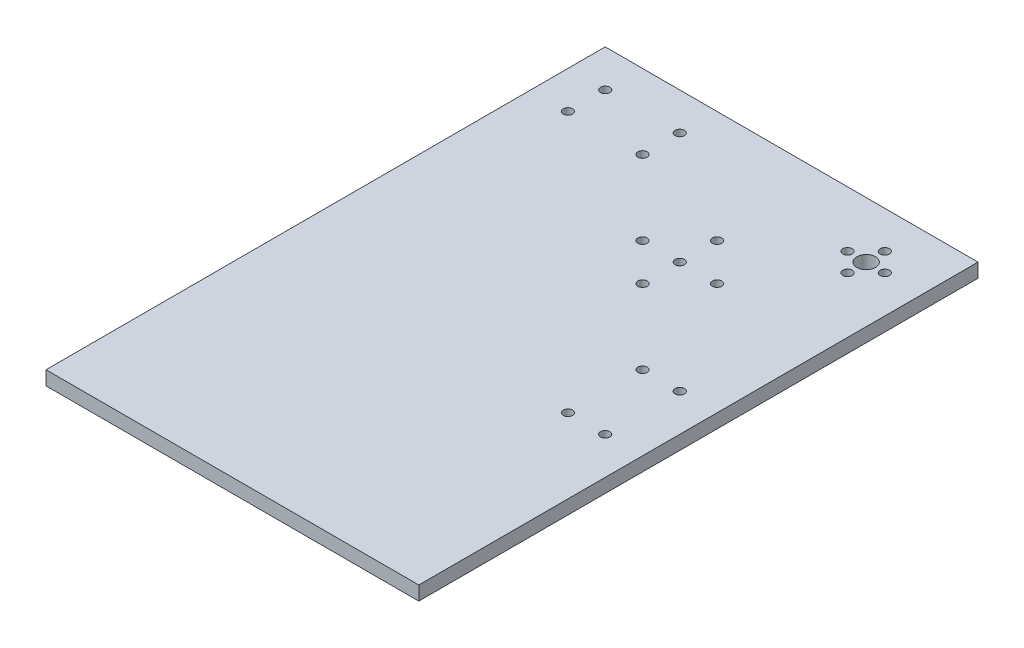
SolidWorks part; units mm, degrees
ref_plane "Front Plane" through (0, 0, 0) normal (0, 0, 1) x (1, 0, 0)
ref_plane "Top Plane" through (0, 0, 0) normal (0, 1, 0) x (1, 0, 0)
ref_plane "Right Plane" through (0, 0, 0) normal (1, 0, 0) x (0, 0, -1)
sketch "Sketch1" plane through (0, 0, 0) normal (0, 1, 0) x (1, 0, 0)
  line L1 (127, -127) -> (-127, -127)
  line L2 (127, -127) -> (127, 127)
  line L3 (127, 127) -> (-127, 127)
  line L4 (-127, -127) -> (-127, 127)
  line L5 (127, -127) -> (-127, 127) construction
  line L6 (127, 127) -> (-127, -127) construction
  point P0 (0, 0)
  dimension "D1" = 254
  dimension "D2" = 254
extrude "Boss-Extrude1" add sketch "Sketch1" along normal blind 9.525
sketch "Sketch2" plane through (0, 9.525, 0) normal (0, 1, 0) x (1, 0, 0)
  line L0 (76.2, -50.8) -> (101.6, -50.8) construction
  line L1 (-101.6, 101.6) -> (-101.6, 76.2) construction
  line L2 (-50.8, 101.6) -> (-50.8, 76.2) construction
  line L3 (76.2, -101.6) -> (101.6, -101.6) construction
  line L4 (25.4, 25.4) -> (88.9, 88.9) construction
  line L5 (127, -127) -> (127, 127) construction
  line L6 (127, 127) -> (-127, 127) construction
  line L7 (88.9, -50.8) -> (88.9, 127) construction
  line L8 (-50.8, 88.9) -> (127, 88.9) construction
  line L9 (88.9, 88.9) -> (25.4, 88.9) construction
  line L10 (88.9, 88.9) -> (88.9, 25.4) construction
  line L11 (88.9, 25.4) -> (25.4, 25.4) construction
  line L12 (25.4, 88.9) -> (25.4, 25.4) construction
  line L13 (25.4, 25.4) -> (25.4, 0) construction
  point P9 (-101.6, 88.9)
  point P17 (88.9, 88.9)
  point P18 (88.9, -101.6)
  point P23 (76.2, 88.9)
  point P24 (88.9, 101.6)
  point P25 (50.8, 25.4)
  point P26 (25.4, 50.8)
  point P27 (25.4, 0)
  point P28 (0, 25.4)
  point P29 (88.9, 76.2)
  point P31 (101.6, 88.9)
  dimension "D1" = 139.7
  dimension "D2" = 25.4
  dimension "D3" = 25.4
  dimension "D4" = 139.7
  dimension "D5" = 25.4
  dimension "D6" = 25.4
  dimension "D7" = 25.4
  dimension "D8" = 25.4
  dimension "D9" = 50.8
  dimension "D10" = 50.8
  dimension "D11" = 63.5
  dimension "D12" = 25.4
  dimension "D13" = 25.4
  dimension "D14" = 25.4
  dimension "D15" = 25.4
  dimension "D16" = 25.4
  dimension "D17" = 12.7
  dimension "D18" = 12.7
  dimension "D19" = 12.7
  dimension "D20" = 12.7
hole_wizard "1/4 (0.25) Diameter Hole1" positions "Sketch3" profile "Sketch4" hole size "1/4" standard "ANSI Inch" end condition through all
sketch "Sketch3" plane through (0, 9.525, 0) normal (0, 1, 0) x (1, 0, 0)
  point P0 (-50.8, 76.2)
  point P3 (-50.8, 101.6)
  point P6 (76.2, -50.8)
  point P9 (101.6, -50.8)
  point P12 (76.2, -101.6)
  point P15 (101.6, -101.6)
  point P18 (-101.6, 76.2)
  point P21 (-101.6, 101.6)
  point P25 (25.4, 50.8)
  point P28 (50.8, 25.4)
  point P32 (25.4, 0)
  point P35 (0, 25.4)
  point P39 (25.4, 25.4)
  point P44 (88.9, 76.2)
  point P47 (76.2, 88.9)
  point P50 (88.9, 101.6)
  point P53 (101.6, 88.9)
sketch "Sketch4" plane through (-50.8, 9.525, -76.2) normal (1, 0, 0) x (0, 0, 1)
  line L0 (0, 0) -> (0, 9.525)
  line L1 (0, 9.525) -> (3.175, 9.525)
  line L2 (3.175, 9.525) -> (3.175, 0)
  line L5 (3.175, 0) -> (0, 0)
  line L11 (0, -6.35) -> (0, 107.95) construction
  dimension "Thru Hole Dia." = 6.35
  dimension "Thru Hole Depth" = 9.525
hole_wizard "1/2 (0.5) Diameter Hole1" positions "Sketch5" profile "Sketch6" hole size "1/2" standard "ANSI Inch" end condition through all
sketch "Sketch5" plane through (0, 9.525, 0) normal (0, 1, 0) x (1, 0, 0)
  point P0 (88.9, 88.9)
sketch "Sketch6" plane through (88.9, 9.525, -88.9) normal (1, 0, 0) x (0, 0, 1)
  line L0 (0, 0) -> (0, 9.525)
  line L1 (0, 9.525) -> (6.35, 9.525)
  line L2 (6.35, 9.525) -> (6.35, 0)
  line L5 (6.35, 0) -> (0, 0)
  line L11 (0, -6.35) -> (0, 107.95) construction
  dimension "Thru Hole Dia." = 12.7
  dimension "Thru Hole Depth" = 9.525
sketch "Sketch8" plane through (0, 0, 127) normal (0, 0, 1) x (1, 0, 0)
  line L4 (-127, 0) -> (127, 0)
  line L5 (127, 0) -> (127, 9.525)
  line L6 (127, 9.525) -> (-127, 9.525)
  line L7 (-127, 9.525) -> (-127, 0)
  line L8 (-127, 0) -> (127, 0)
  line L9 (127, 0) -> (127, 9.525)
  line L10 (127, 9.525) -> (-127, 9.525)
  line L11 (-127, 9.525) -> (-127, 0)
  dimension "D1" = 0
extrude "Boss-Extrude2" add sketch "Sketch8" along normal blind 127
